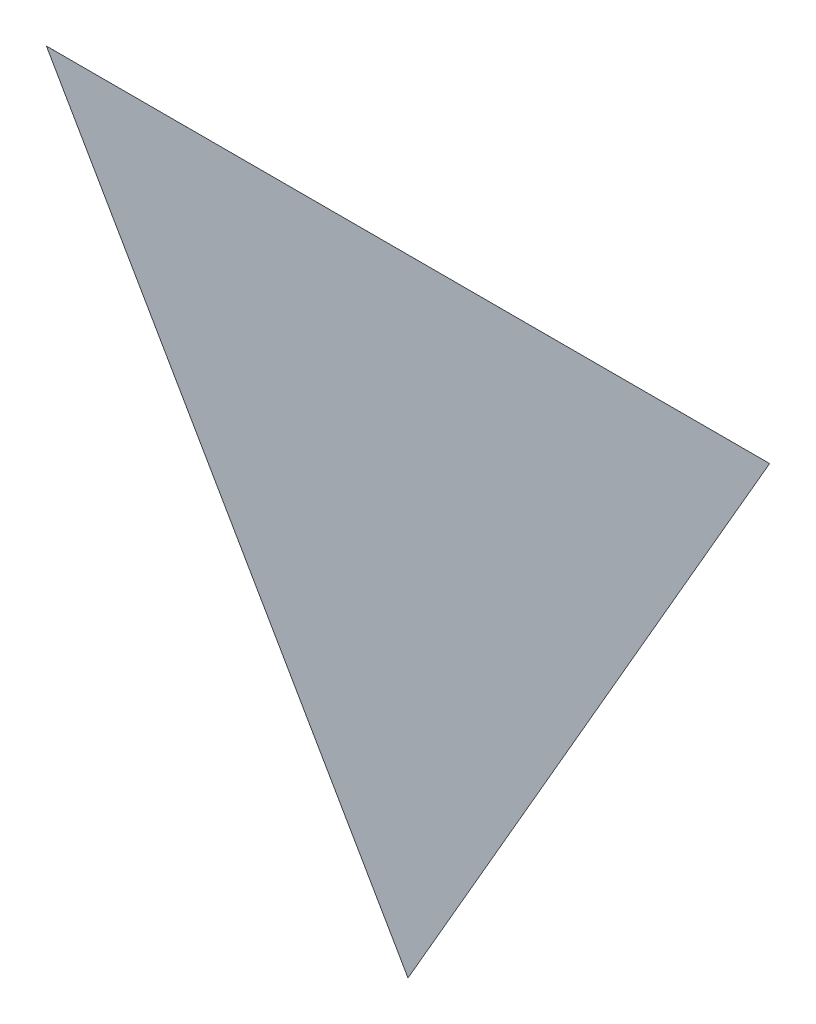
SolidWorks part; units mm, degrees
ref_plane "Alzado" through (0, 0, 0) normal (0, 0, 1) x (1, 0, 0)
ref_plane "Planta" through (0, 0, 0) normal (0, 1, 0) x (1, 0, 0)
ref_plane "Vista lateral" through (0, 0, 0) normal (1, 0, 0) x (0, 0, -1)
sketch "Croquis1" plane through (0, 0, 0) normal (0, 0, 1) x (1, 0, 0)
  line L0 (-60.6986, 26.0026) -> (-35.6986, 26.0026)
  line L1 (-35.6986, 26.0026) -> (-48.1986, 4.3519)
  line L2 (-48.1986, 4.3519) -> (-60.6986, 26.0026)
  dimension "D1" = 25
  dimension "D2" = 25
  dimension "D3" = 25
extrude "Saliente-Extruir1" add sketch "Croquis1" along normal blind 0.0001
